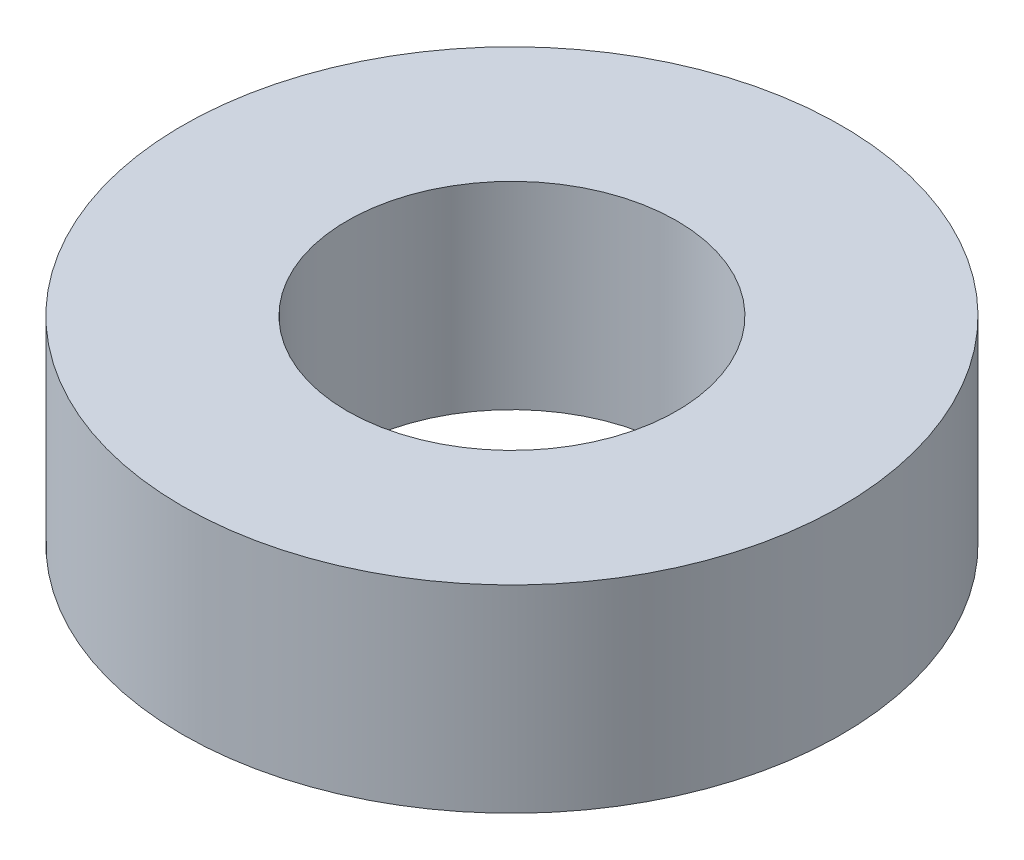
SolidWorks part; units mm, degrees
ref_plane "Front Plane" through (0, 0, 0) normal (0, 0, 1) x (1, 0, 0)
ref_plane "Top Plane" through (0, 0, 0) normal (0, 1, 0) x (1, 0, 0)
ref_plane "Right Plane" through (0, 0, 0) normal (1, 0, 0) x (0, 0, -1)
sketch "Sketch1" plane through (0, 0, 0) normal (0, 1, 0) x (1, 0, 0)
  circle A0 centre (0, 0) radius 2.5
  circle A1 centre (0, 0) radius 5
  dimension "D1" = 5
  dimension "D2" = 10
extrude "Boss-Extrude1" add sketch "Sketch1" along normal blind 3
